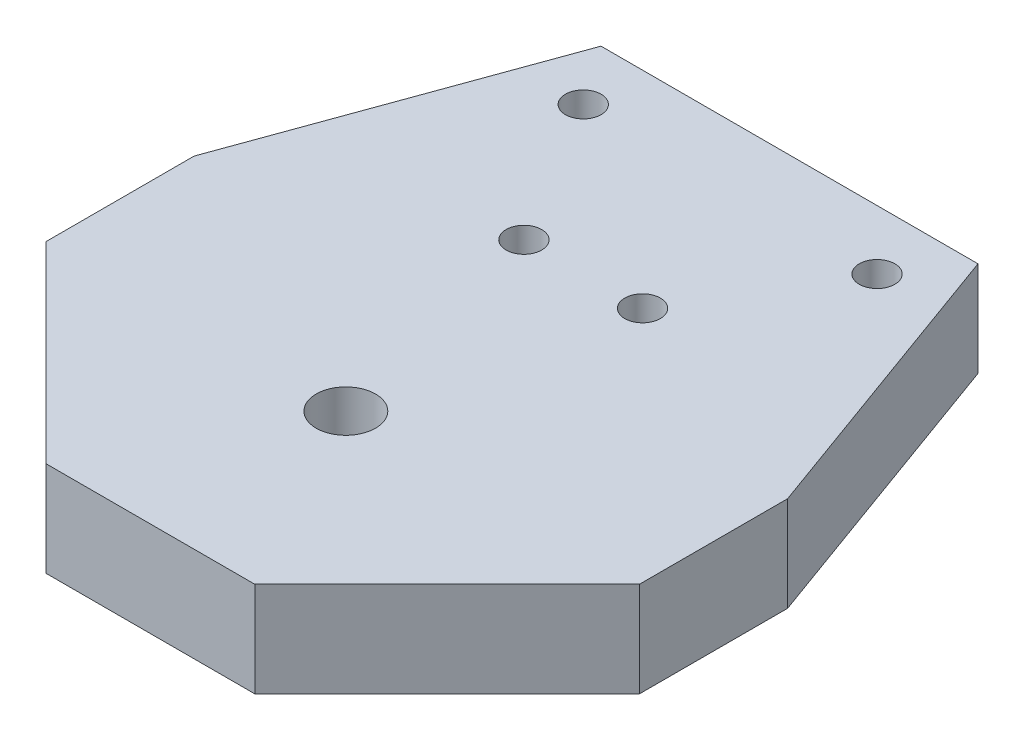
SolidWorks part; units mm, degrees
ref_plane "Front Plane" through (0, 0, 0) normal (0, 0, 1) x (1, 0, 0)
ref_plane "Top Plane" through (0, 0, 0) normal (0, 1, 0) x (1, 0, 0)
ref_plane "Right Plane" through (0, 0, 0) normal (1, 0, 0) x (0, 0, -1)
sketch "Sketch1" plane through (0, 0, 0) normal (0, 1, 0) x (1, 0, 0)
  line L0 (-5, 0) -> (5, 0) construction
  line L1 (0, 17.3789) -> (0, -20) construction
  line L2 (0, -20) -> (0, -36.47) construction
  line L3 (-8.795, -36.47) -> (8.795, -36.47)
  line L4 (-8.795, -36.47) -> (-25.0019, -20.2631)
  line L5 (-25.0019, -20.2631) -> (-25.0019, -7.7831)
  line L6 (-25.0019, -7.7831) -> (25.0019, -7.7831) construction
  line L7 (8.795, -36.47) -> (25.0019, -20.2631)
  line L8 (25.0019, -20.2631) -> (25.0019, -7.7831)
  line L12 (25.0019, -7.7831) -> (15.8825, 17.3789)
  line L13 (5, 6) -> (5, 0) construction
  line L14 (5, 0) -> (12.3764, 12.3789) construction
  line L15 (15.8825, 17.3789) -> (-15.8825, 17.3789)
  line L16 (-25.0019, -7.7831) -> (-15.8825, 17.3789)
  circle A0 centre (-5, 0) radius 1.5
  circle A1 centre (5, 0) radius 1.5
  circle A2 centre (0, -20) radius 2.5
  circle A3 centre (12.3764, 12.3789) radius 1.5
  circle A4 centre (-12.3764, 12.3789) radius 1.5
  point P3 (0, 0)
  point P12 (0, -36.47)
  point P18 (0, -7.7831)
  point P19 (0, 19.6484)
  dimension "D2" = 3
  dimension "D3" = 3
  dimension "D4" = 5
  dimension "D13" = 3
  dimension "D1" = 10
  dimension "D5" = 20
  dimension "D6" = 17.59
  dimension "16.47" = 16.47
  dimension "D7" = 22.92
  dimension "D8" = 135
  dimension "D9" = 12.48
  dimension "D10" = 5
  dimension "D11" = 120.79
  dimension "D12" = 14.41
  dimension "D14" = 5
extrude "Boss-Extrude1" add sketch "Sketch1" along normal blind 8
